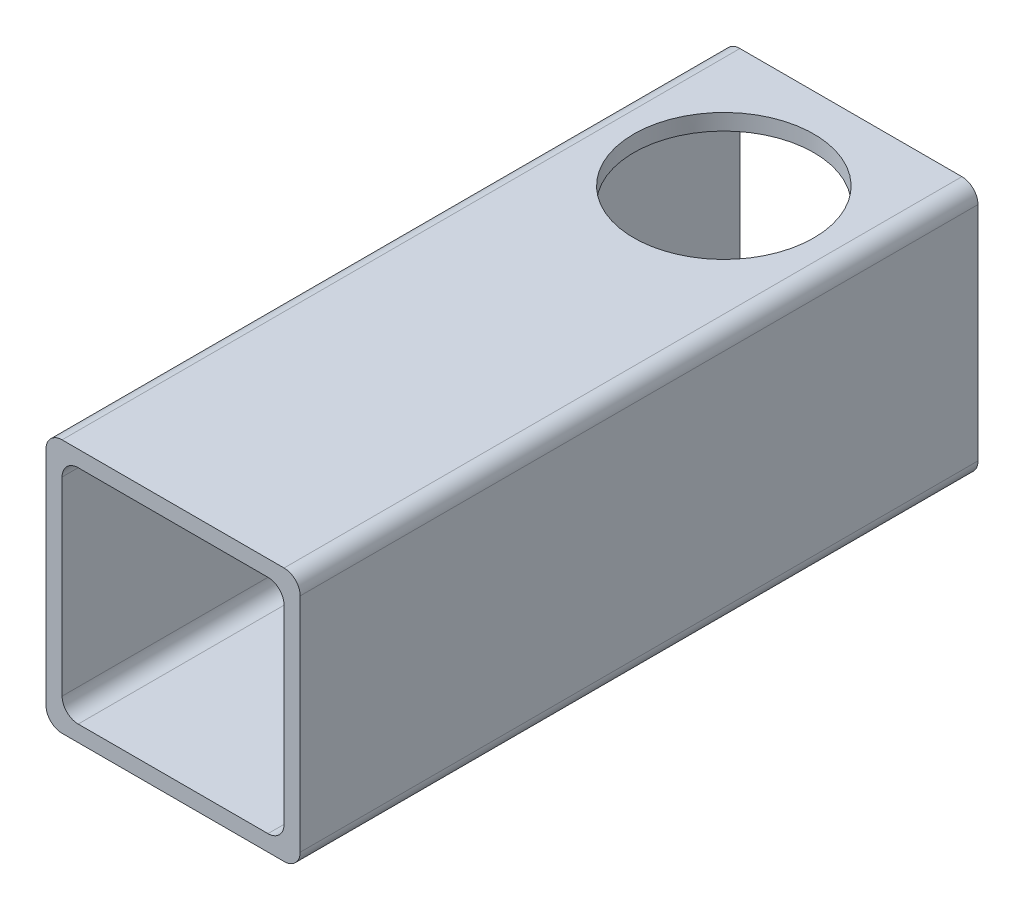
SolidWorks part; units mm, degrees
material "ASTM A36 Steel"
ref_plane "Front Plane" through (0, 0, 0) normal (0, 0, 1) x (1, 0, 0)
ref_plane "Top Plane" through (0, 0, 0) normal (0, 1, 0) x (1, 0, 0)
ref_plane "Right Plane" through (0, 0, 0) normal (1, 0, 0) x (0, 0, -1)
sketch "Sketch1" plane through (0, 0, 0) normal (0, 0, 1) x (1, 0, 0)
  line L0 (-14.224, -16.637) -> (14.224, -16.637)
  line L1 (-16.637, -14.224) -> (-16.637, 14.224)
  line L2 (14.224, 16.637) -> (-14.224, 16.637)
  line L3 (16.637, 14.224) -> (16.637, -14.224)
  line L4 (-16.637, -19.05) -> (16.637, -19.05)
  line L5 (-19.05, -16.637) -> (-19.05, 16.637)
  line L6 (16.637, 19.05) -> (-16.637, 19.05)
  line L7 (19.05, 16.637) -> (19.05, -16.637)
  line L10 (-16.637, 0) -> (16.637, 0) construction
  arc A0 (19.05, 16.637) -> (16.637, 19.05) centre (16.637, 16.637) ccw
  arc A1 (16.637, -19.05) -> (19.05, -16.637) centre (16.637, -16.637) ccw
  arc A2 (-19.05, -16.637) -> (-16.637, -19.05) centre (-16.637, -16.637) ccw
  arc A3 (-16.637, 19.05) -> (-19.05, 16.637) centre (-16.637, 16.637) ccw
  arc A4 (-14.224, 16.637) -> (-16.637, 14.224) centre (-14.224, 14.224) ccw
  arc A5 (16.637, 14.224) -> (14.224, 16.637) centre (14.224, 14.224) ccw
  arc A6 (14.224, -16.637) -> (16.637, -14.224) centre (14.224, -14.224) ccw
  arc A7 (-16.637, -14.224) -> (-14.224, -16.637) centre (-14.224, -14.224) ccw
extrude "Boss-Extrude1" add sketch "Sketch1" along normal blind 101.6
sketch "Sketch2" plane through (0, 0, 0) normal (0, 1, 0) x (1, 0, 0)
  line L0 (0, -20.955) -> (0, 20.955) construction
  line L1 (-20.955, 0) -> (20.955, 0) construction
  circle A0 centre (0, -19.05) radius 13.4938
  dimension "D1" = 26.9875
  dimension "D2" = 19.05
extrude "Cut-Extrude1" cut sketch "Sketch2" against normal mid plane 457.2
